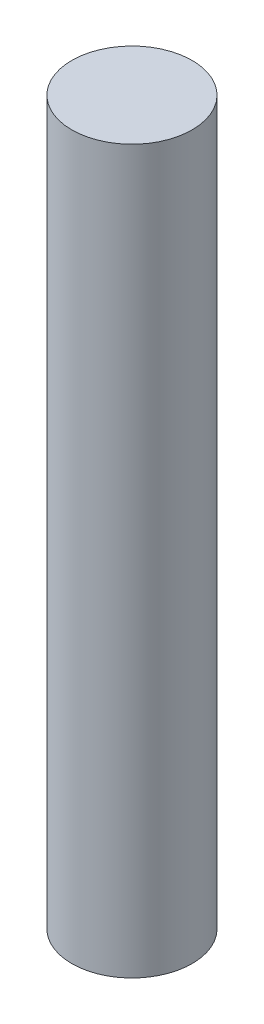
SolidWorks part; units mm, degrees
ref_plane "Спереди" through (0, 0, 0) normal (0, 0, 1) x (1, 0, 0)
ref_plane "Сверху" through (0, 0, 0) normal (0, 1, 0) x (1, 0, 0)
ref_plane "Справа" through (0, 0, 0) normal (1, 0, 0) x (0, 0, -1)
sketch "Эскиз1" plane through (0, 0, 0) normal (0, 1, 0) x (1, 0, 0)
  circle A0 centre (0, 0) radius 2.5
extrude "Бобышка-Вытянуть1" add sketch "Эскиз1" along normal blind 30
